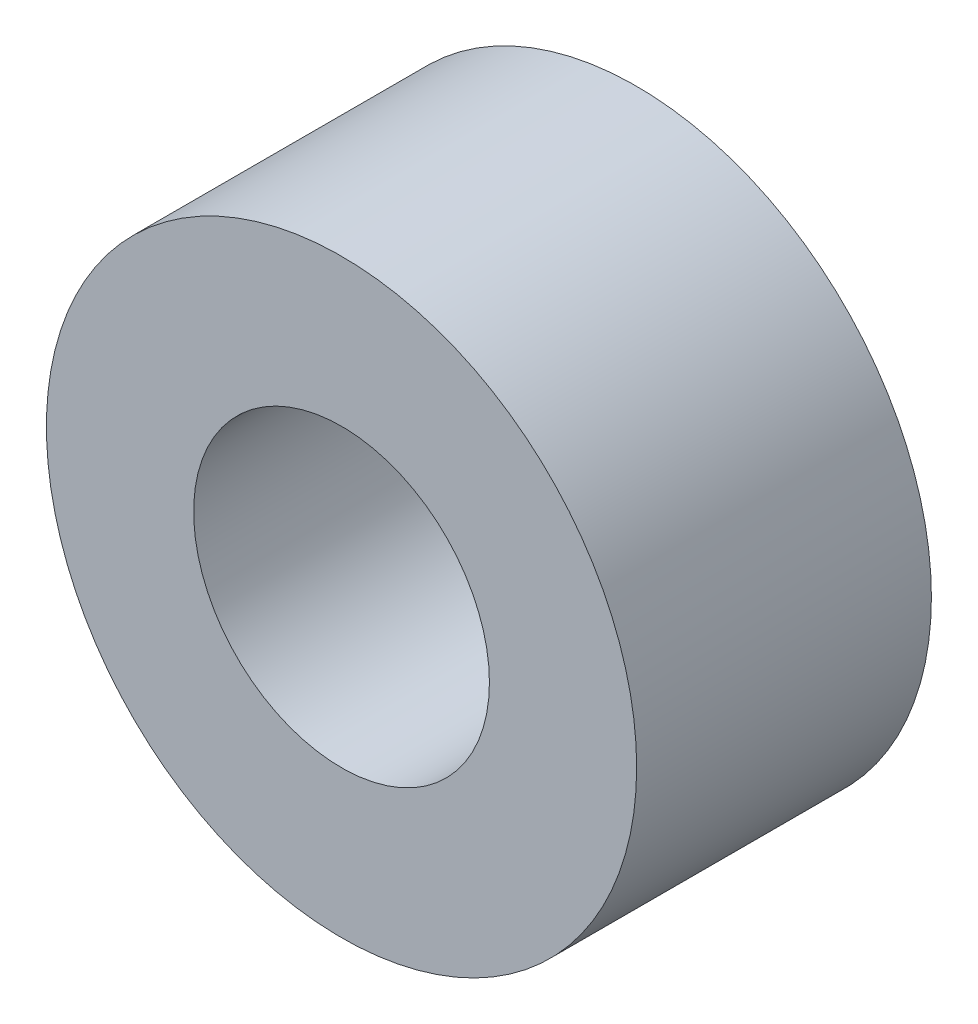
SolidWorks part; units mm, degrees
ref_plane "Front Plane" through (0, 0, 0) normal (0, 0, 1) x (1, 0, 0)
ref_plane "Top Plane" through (0, 0, 0) normal (0, 1, 0) x (1, 0, 0)
ref_plane "Right Plane" through (0, 0, 0) normal (1, 0, 0) x (0, 0, -1)
sketch "Sketch1" plane through (0, 0, 0) normal (0, 0, 1) x (1, 0, 0)
  circle A0 centre (0, 0) radius 60.078
extrude "Extrude1" add sketch "Sketch1" along normal blind 60
sketch "Sketch2" plane through (0, 0, 60) normal (0, 0, 1) x (1, 0, 0)
  circle A0 centre (0, 0) radius 30.106
extrude "Cut-Extrude1" cut sketch "Sketch2" against normal blind 60
